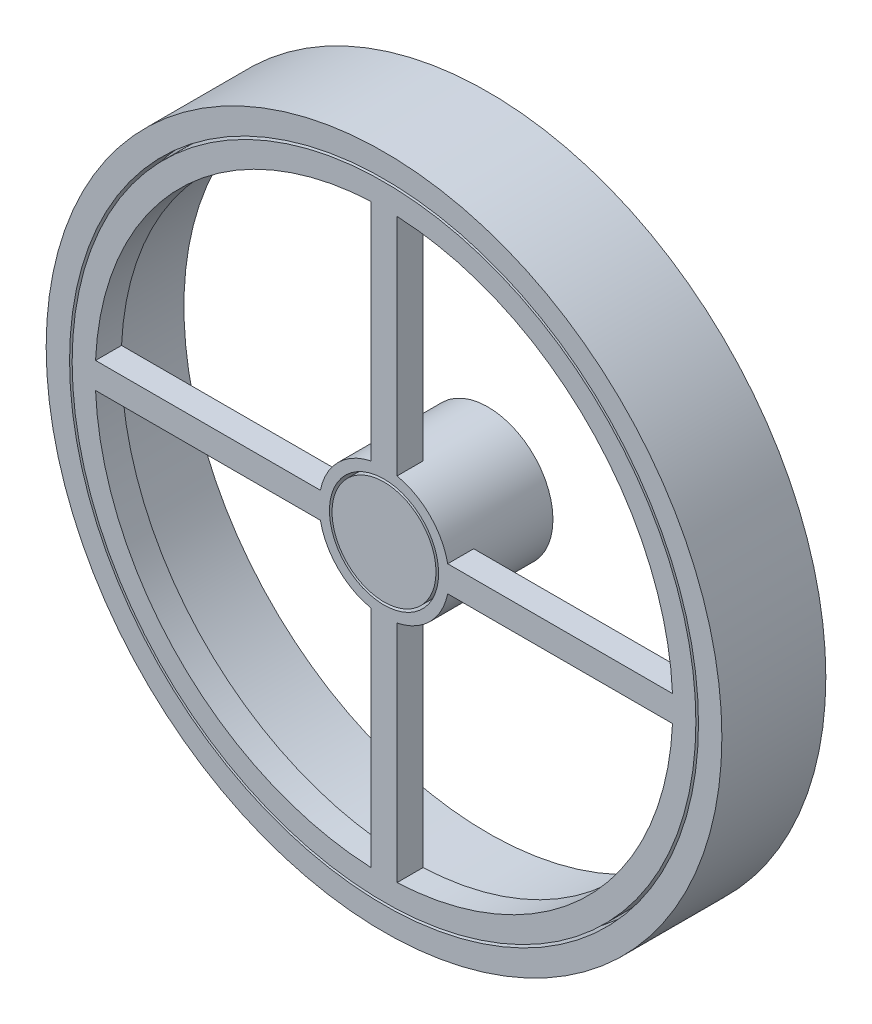
SolidWorks part; units mm, degrees
ref_plane "Front Plane" through (0, 0, 0) normal (0, 0, 1) x (1, 0, 0)
ref_plane "Top Plane" through (0, 0, 0) normal (0, 1, 0) x (1, 0, 0)
ref_plane "Right Plane" through (0, 0, 0) normal (1, 0, 0) x (0, 0, -1)
sketch "Sketch2" plane through (0, 0, 0) normal (0, 0, 1) x (1, 0, 0)
  circle A0 centre (0, 0) radius 65
  dimension "D1" = 130
extrude "Boss-Extrude1" add sketch "Sketch2" along normal blind 20
sketch "Sketch3" plane through (0, 0, 20) normal (0, 0, 1) x (1, 0, 0)
  circle A0 centre (0, 0) radius 58.5
  dimension "D1" = 117
extrude "Cut-Extrude1" cut sketch "Sketch3" against normal blind 20
sketch "Sketch4" plane through (0, 0, 20) normal (0, 0, 1) x (1, 0, 0)
  circle A0 centre (0, 0) radius 60.5
  circle A1 centre (0, 0) radius 60
  dimension "D1" = 120
  dimension "D2" = 121
extrude "Cut-Extrude3" cut sketch "Sketch4" against normal blind 5
sketch "Sketch5" plane through (0, 0, 20) normal (0, 0, 1) x (1, 0, 0)
  circle A0 centre (0, 0) radius 10
  dimension "D1" = 20
extrude "Boss-Extrude2" add sketch "Sketch5" against normal blind 20 separate body
sketch "Sketch6" plane through (0, 0, 20) normal (0, 0, 1) x (1, 0, 0)
  circle A0 centre (0, 0) radius 10.5
  circle A1 centre (0, 0) radius 58.5
  dimension "D1" = 117
extrude "Boss-Extrude3" add sketch "Sketch6" against normal blind 5
sketch "Sketch8" plane through (0, 0, 20) normal (0, 0, 1) x (1, 0, 0)
  line L4 (0, 60) -> (0, -60) construction
  line L5 (-60, 0) -> (60, 0) construction
  line L7 (-2.5, 12.2474) -> (-2.5, 55.5)
  line L8 (2.5, 12.2474) -> (2.5, 55.5)
  line L10 (-2.5, 12.2474) -> (-2.5, 55.5)
  line L11 (2.5, 12.2474) -> (2.5, 55.5)
  line L14 (-2.5, -12.2474) -> (-2.5, -55.5)
  line L15 (2.5, -12.2474) -> (2.5, -55.5)
  line L17 (12.2474, 2.5) -> (55.5, 2.5)
  line L18 (12.2474, -2.5) -> (55.5, -2.5)
  line L20 (12.2474, 2.5) -> (55.5, 2.5)
  line L21 (12.2474, -2.5) -> (55.5, -2.5)
  line L23 (-12.2474, -2.5) -> (-55.5, -2.5)
  line L25 (-12.2474, 2.5) -> (-55.5, 2.5)
  arc A0 (-2.5, 12.2474) -> (-12.2474, 2.5) centre (0, 0) ccw
  circle A1 centre (0, 0) radius 60 construction
  circle A2 centre (0, 0) radius 60 construction
  arc A3 (-55.5, -2.5) -> (-2.5, -55.5) centre (0, 0) ccw
  arc A4 (-12.2474, -2.5) -> (-2.5, -12.2474) centre (0, 0) ccw
  arc A5 (12.2474, 2.5) -> (2.5, 12.2474) centre (0, 0) ccw
  arc A6 (2.5, -12.2474) -> (12.2474, -2.5) centre (0, 0) ccw
  arc A7 (2.5, -55.5) -> (55.5, -2.5) centre (0, 0) ccw
  arc A8 (55.5, 2.5) -> (2.5, 55.5) centre (0, 0) ccw
  arc A9 (-2.5, 55.5) -> (-55.5, 2.5) centre (0, 0) ccw
  dimension "D2" = 25
  dimension "D4" = 5
  dimension "D3" = 55.5563
  dimension "D1" = 5
extrude "Cut-Extrude4" cut sketch "Sketch8" against normal blind 5 contours L7 A9 L25 A0 | L15 A7 L18 A6 | L17 A8 L8 A5 | A4 L23 A3 L14
sketch "Sketch9" plane through (0, 0, 15) normal (0, 0, -1) x (-1, 0, 0)
  circle A0 centre (0, 0) radius 10
  circle A1 centre (0, 0) radius 10 construction
  circle A2 centre (0, 0) radius 12.5
  arc A3 (12.2474, 2.5) -> (2.5, 12.2474) centre (0, 0) ccw construction
extrude "Boss-Extrude4" add sketch "Sketch9" along normal up to surface (15 mm away) up to face at (10, 0, 0)
